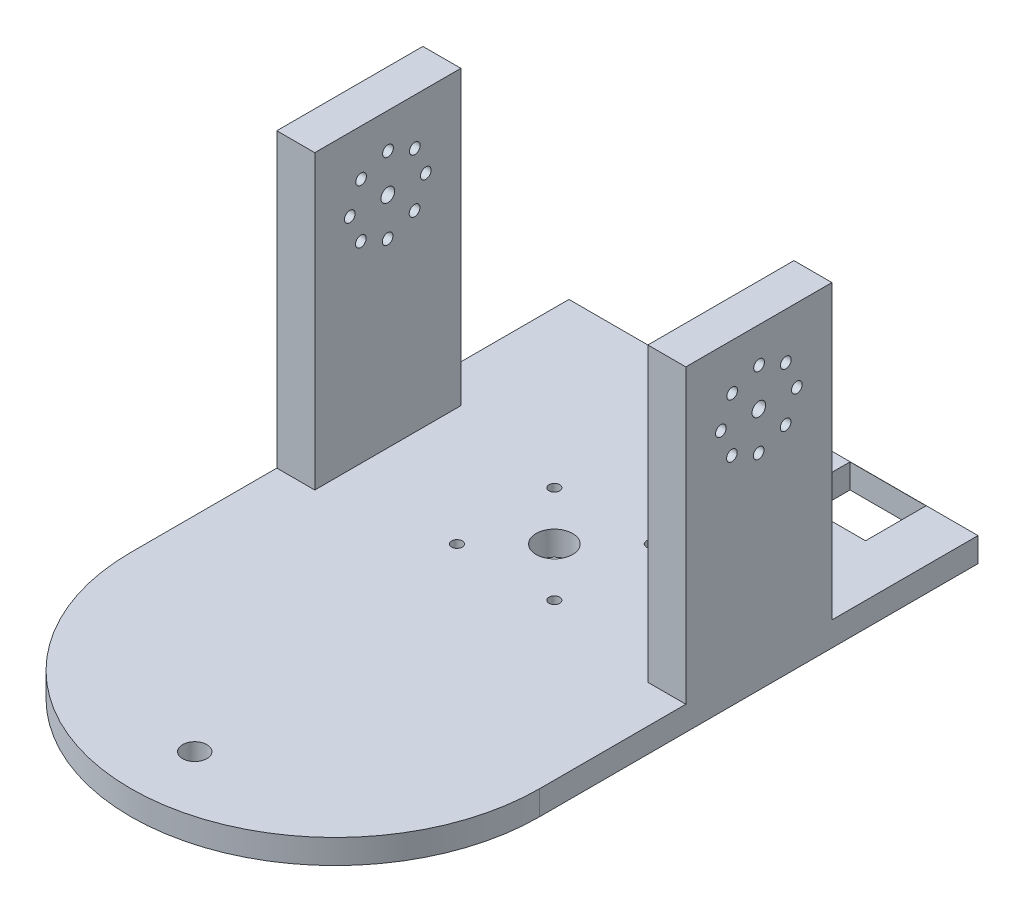
SolidWorks part; units mm, degrees
ref_plane "Front Plane" through (0, 0, 0) normal (0, 0, 1) x (1, 0, 0)
ref_plane "Top Plane" through (0, 0, 0) normal (0, 1, 0) x (1, 0, 0)
ref_plane "Right Plane" through (0, 0, 0) normal (1, 0, 0) x (0, 0, -1)
sketch "Sketch1" plane through (0, 0, 0) normal (0, 1, 0) x (1, 0, 0)
  line L0 (-53.34, 0) -> (53.34, 0) construction
  line L1 (-53.34, 57.15) -> (53.34, 57.15)
  line L2 (-53.34, 57.15) -> (-53.34, -57.15)
  line L3 (0, 0) -> (0, -110.49) construction
  line L4 (53.34, 57.15) -> (53.34, -57.15)
  line L5 (-53.34, 57.15) -> (53.34, -57.15) construction
  line L6 (-53.34, -57.15) -> (53.34, 57.15) construction
  line L7 (0, -57.15) -> (0, 57.15) construction
  line L9 (-12.7, 12.7) -> (12.7, 12.7) construction
  line L10 (-12.7, 12.7) -> (-12.7, -12.7) construction
  line L11 (-12.7, -12.7) -> (12.7, -12.7) construction
  line L12 (12.7, 12.7) -> (12.7, -12.7) construction
  line L13 (-12.7, 12.7) -> (12.7, -12.7) construction
  line L14 (-12.7, -12.7) -> (12.7, 12.7) construction
  circle A0 centre (0, 0) radius 4.572
  circle A1 centre (-12.7, -12.7) radius 1.397
  circle A2 centre (-12.7, 12.7) radius 1.397
  circle A3 centre (12.7, 12.7) radius 1.397
  circle A4 centre (12.7, -12.7) radius 1.397
  arc A5 (53.34, -57.15) -> (-53.34, -57.15) centre (0, -57.15) cw
  circle A6 centre (0, -93.7912) radius 3.175
  point P0 (0, 0)
  point P11 (0, 0)
  point P14 (0, 0)
  point P22 (0, 0)
  point P25 (0, 0)
  point P28 (0, 0)
  point P31 (0, 0)
  dimension "D3" = 25.4
  dimension "D4" = 25.4
  dimension "D5" = 2.794
  dimension "D7" = 6.35
  dimension "D1" = 114.3
  dimension "D2" = 106.68
  dimension "D6" = 4
extrude "Boss-Extrude1" add sketch "Sketch1" along normal blind 6.35
hole_wizard "3/8 (0.375) Diameter Slot1" positions "Sketch5" profile "Sketch4" size "3/8" standard "ANSI Inch" slot yes end condition through all
sketch "Sketch5" plane through (0, 6.35, 0) normal (0, 1, 0) x (1, 0, 0)
  point P0 (0, 0)
  point P3 (0, 0)
sketch "Sketch4" plane through (0, 6.35, 0) normal (1, 0, 0) x (0, 0, 1)
  line L0 (0, 0) -> (0, 6.35)
  line L1 (0, 6.35) -> (4.7625, 6.35)
  line L2 (4.7625, 6.35) -> (4.7625, 0)
  line L5 (4.7625, 0) -> (0, 0)
  line L11 (0, -6.35) -> (0, 107.95) construction
  dimension "Thru Hole Dia." = 9.525
  dimension "Thru Hole Depth" = 6.35
sketch "Sketch6" plane through (0, 6.35, 0) normal (0, 1, 0) x (1, 0, 0)
  line L1 (-53.34, 19.05) -> (-43.434, 19.05)
  line L2 (-53.34, 19.05) -> (-53.34, -19.05)
  line L3 (-53.34, -19.05) -> (-43.434, -19.05)
  line L4 (-43.434, 19.05) -> (-43.434, -19.05)
  line L5 (-19.05, 19.05) -> (19.05, 19.05) construction
  line L6 (53.34, 19.05) -> (43.434, 19.05)
  line L7 (53.34, 19.05) -> (53.34, -19.05)
  line L8 (53.34, -19.05) -> (43.434, -19.05)
  line L9 (43.434, 19.05) -> (43.434, -19.05)
  line L10 (-19.05, 19.05) -> (-19.05, -19.05) construction
  line L11 (-53.34, 57.15) -> (-53.34, -57.15) construction
  line L12 (53.34, 57.15) -> (53.34, -57.15) construction
  line L13 (-19.05, -19.05) -> (19.05, -19.05) construction
  line L14 (-53.34, 0) -> (53.34, 0) construction
  line L15 (19.05, 19.05) -> (19.05, -19.05) construction
  line L16 (-19.05, 19.05) -> (19.05, -19.05) construction
  line L17 (-19.05, -19.05) -> (19.05, 19.05) construction
  point P12 (0, 0)
  point P24 (0, 0)
  point P27 (0, 0)
  point P30 (0, 0)
  point P33 (0, 0)
  dimension "D1" = 38.1
  dimension "D2" = 86.868
  dimension "D3" = 19.05
  dimension "D4" = 9.906
  dimension "D6" = 38.1
  dimension "D7" = 38.1
  dimension "D9" = 4
extrude "Boss-Extrude2" add sketch "Sketch6" along normal blind 76.2
sketch "Sketch7" plane through (-53.34, 0, 0) normal (-1, 0, 0) x (0, 0, 1)
  line L0 (0, 82.55) -> (0, 0) construction
  line L1 (-19.05, 82.55) -> (19.05, 82.55) construction
  line L2 (-57.15, 0) -> (57.15, 0) construction
  line L3 (-19.05, 44.45) -> (19.05, 44.45) construction
  line L4 (-19.05, 82.55) -> (-19.05, 6.35) construction
  line L5 (19.05, 82.55) -> (19.05, 6.35) construction
  line L6 (-19.05, 63.5) -> (19.05, 63.5) construction
  circle A0 centre (0, 63.5) radius 12.7 construction
  circle A1 centre (-9.906, 63.4552) radius 1.397
  circle A2 centre (0, 63.5) radius 1.7859
  circle A4 centre (-7.0363, 70.4729) radius 1.397
  circle A5 centre (-0.0448, 73.406) radius 1.397
  circle A6 centre (6.9729, 70.5363) radius 1.397
  circle A7 centre (9.906, 63.5448) radius 1.397
  circle A8 centre (7.0363, 56.5271) radius 1.397
  circle A9 centre (0.0448, 53.594) radius 1.397
  circle A10 centre (-6.9729, 56.4637) radius 1.397
  point P14 (-0.4738, 53.6762)
  point P15 (-7.3886, 56.5404)
  point P16 (-9.906, 63.4552)
  point P17 (-7.3886, 70.37)
  point P18 (-0.4738, 73.2342)
  point P19 (6.441, 70.37)
  point P20 (9.3052, 63.4552)
  point P21 (6.441, 56.5404)
  point P45 (0, 63.5)
  dimension "D2" = 25.4
  dimension "D1" = 19.05
  dimension "D3" = 9.906
  dimension "D5" = 8
extrude "Cut-Extrude1" cut sketch "Sketch7" against normal through all
sketch "Sketch8" plane through (0, 6.35, 0) normal (0, 1, 0) x (1, 0, 0)
  line L1 (20.0057, 57.1034) -> (39.8452, 57.1034)
  line L2 (20.0057, 57.1034) -> (20.0057, 41.3111)
  line L3 (20.0057, 41.3111) -> (39.8452, 41.3111)
  line L4 (39.8452, 57.1034) -> (39.8452, 41.3111)
  line L5 (20.0057, 57.1034) -> (39.8452, 41.3111)
  line L6 (20.0057, 41.3111) -> (39.8452, 57.1034)
  point P0 (29.9254, 49.2073)
extrude "Cut-Extrude2" cut sketch "Sketch8" against normal blind 10.16 contours L2 L6 L5 | L6 L3 L5 | L6 L5 L4 | L5 L6 L1
